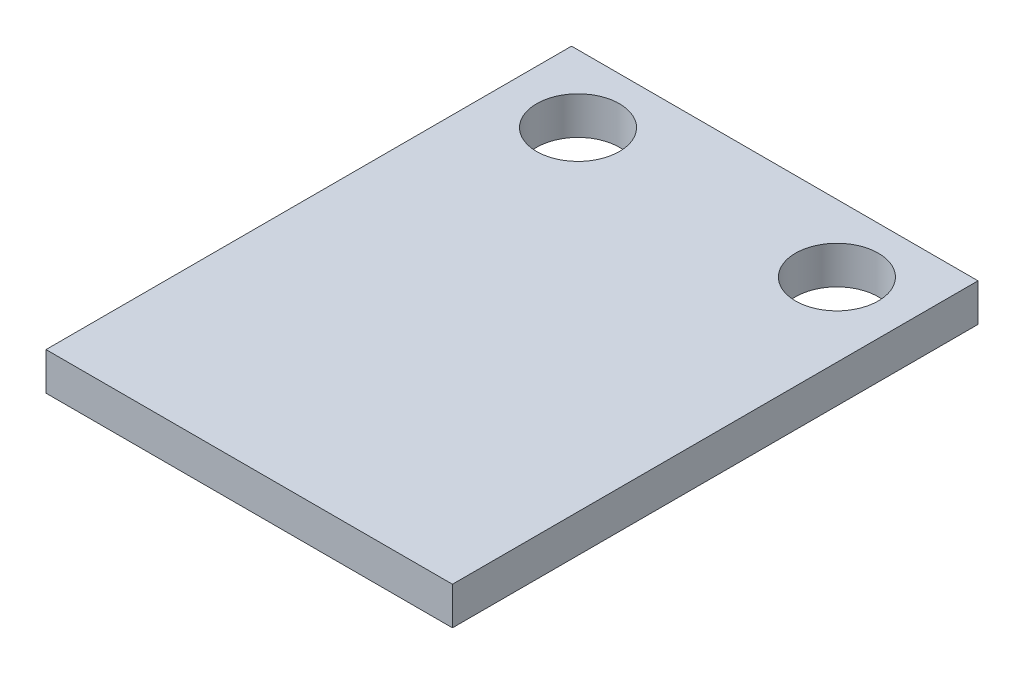
SolidWorks part; units mm, degrees
ref_plane "Front Plane" through (0, 0, 0) normal (0, 0, 1) x (1, 0, 0)
ref_plane "Top Plane" through (0, 0, 0) normal (0, 1, 0) x (1, 0, 0)
ref_plane "Right Plane" through (0, 0, 0) normal (1, 0, 0) x (0, 0, -1)
sketch "Sketch1" plane through (0, 0, 0) normal (0, 1, 0) x (1, 0, 0)
  line L0 (0, 0) -> (0, 12.5913) construction
  line L1 (-7.85, -10.15) -> (7.85, -10.15)
  line L2 (-7.85, -10.15) -> (-7.85, 10.15)
  line L3 (-7.85, 10.15) -> (7.85, 10.15)
  line L4 (7.85, -10.15) -> (7.85, 10.15)
  line L5 (-7.85, -10.15) -> (7.85, 10.15) construction
  line L6 (-7.85, 10.15) -> (7.85, -10.15) construction
  circle A0 centre (-5, 7.55) radius 1.6
  circle A1 centre (5, 7.55) radius 1.6
  point P0 (0, 0)
  dimension "D3" = 3.2
  dimension "D1" = 20.3
  dimension "D2" = 15.7
  dimension "D4" = 10
  dimension "D5" = 2.6
extrude "Boss-Extrude1" add sketch "Sketch1" along normal blind 1.46
